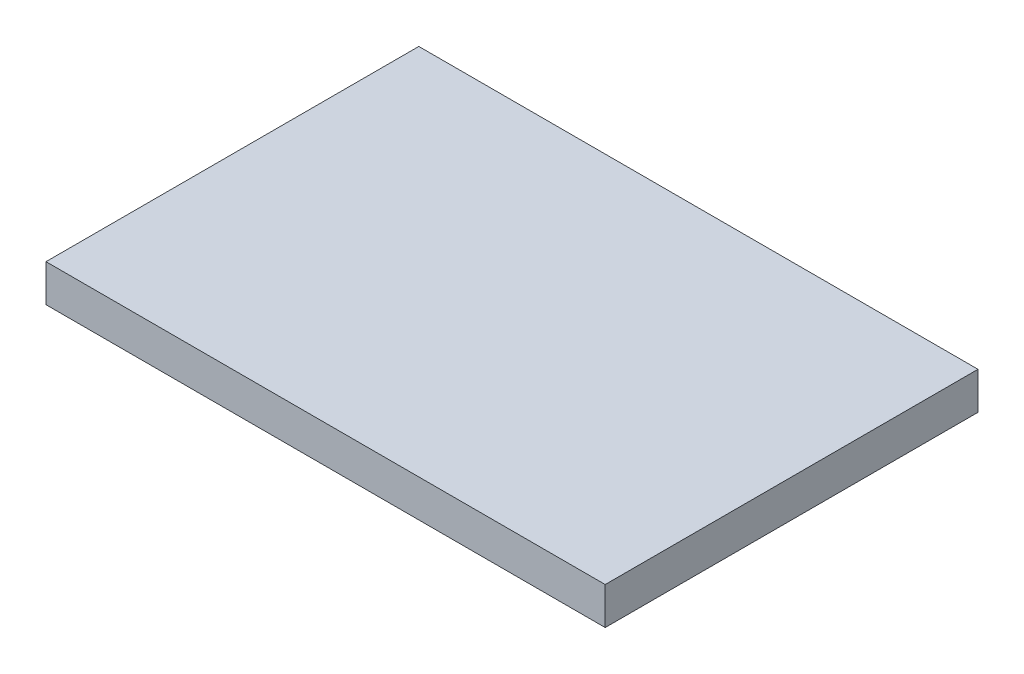
SolidWorks part; units mm, degrees
ref_plane "Plan de face" through (0, 0, 0) normal (0, 0, 1) x (1, 0, 0)
ref_plane "Plan de dessus" through (0, 0, 0) normal (0, 1, 0) x (1, 0, 0)
ref_plane "Plan de droite" through (0, 0, 0) normal (1, 0, 0) x (0, 0, -1)
sketch "Esquisse1" plane through (0, 0, 0) normal (0, 1, 0) x (1, 0, 0)
  line L1 (0, 0) -> (150, 0)
  line L2 (0, 0) -> (0, 100)
  line L3 (0, 100) -> (150, 100)
  line L4 (150, 0) -> (150, 100)
  dimension "D1" = 100
  dimension "D2" = 150
extrude "Boss.-Extru.1" add sketch "Esquisse1" along normal blind 10
